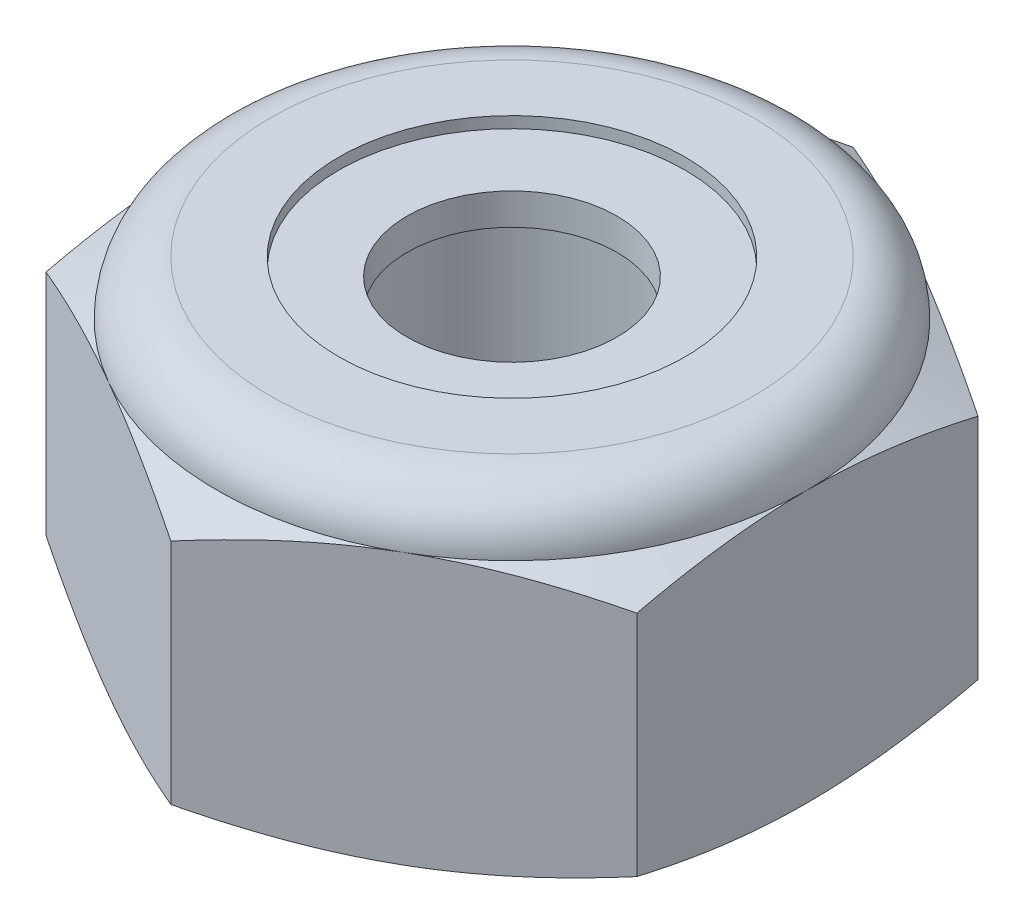
SolidWorks part; units mm, degrees
ref_plane "Front" through (0, 0, 0) normal (0, 0, 1) x (1, 0, 0)
ref_plane "Top" through (0, 0, 0) normal (0, 1, 0) x (1, 0, 0)
ref_plane "Right" through (0, 0, 0) normal (1, 0, 0) x (0, 0, -1)
sketch "Sketch1" plane through (0, 0, 0) normal (0, 1, 0) x (1, 0, 0)
  line L1 (0, 4.5827) -> (-3.9688, 2.2914)
  line L2 (-3.9688, 2.2914) -> (-3.9688, -2.2914)
  line L3 (-3.9688, -2.2914) -> (0, -4.5827)
  line L4 (0, -4.5827) -> (3.9688, -2.2914)
  line L5 (3.9688, -2.2914) -> (3.9687, 2.2914)
  line L6 (3.9687, 2.2914) -> (0, 4.5827)
  circle A0 centre (0, 0) radius 3.9688 construction
  dimension "Hex Flats" = 7.9375
extrude "Extrude1" add sketch "Sketch1" along normal blind 4.3656
sketch "Sketch2" plane through (0, 0, 0) normal (1, 0, 0) x (0, 0, -1)
  line L0 (-1.7526, 0) -> (-1.7526, 4.3656) construction
  line L1 (0, 0) -> (1.7526, 0)
  line L2 (0, 0) -> (0, 4.3656)
  line L3 (0, 4.3656) -> (1.7526, 4.3656)
  line L4 (1.7526, 0) -> (1.7526, 4.3656)
  line L5 (-2.2914, 4.3656) -> (2.2914, 4.3656) construction
  line L7 (0, -1.7526) -> (0, 0) construction
  dimension "Thread Dia" = 3.5052
revolve "Revolve1" add sketch "Sketch2" angle 360 about L7
sketch "Sketch3" plane through (0, 0, 0) normal (1, 0, 0) x (0, 0, -1)
  line L0 (1.7526, 4.3656) -> (-1.7526, 4.3656) construction
  line L1 (-1.7526, 4.3656) -> (-1.7526, 3.5719) construction
  line L2 (-1.7526, 3.5719) -> (1.7526, 4.3656) construction
  line L3 (1.7526, 4.3656) -> (1.7745, 4.2689) construction
  line L4 (1.7745, 4.2689) -> (1.9279, 3.5915)
  line L5 (1.9279, 3.5915) -> (1.4541, 3.7385)
  line L6 (1.4541, 3.7385) -> (1.4103, 3.932)
  line L7 (1.4103, 3.932) -> (1.7745, 4.2689)
  line L8 (1.4322, 3.8353) -> (1.8512, 3.9302) construction
  line L9 (1.7526, 4.3656) -> (1.7526, 3.9078) construction
  line L10 (1.7526, 3.9078) -> (-1.7526, 3.1141) construction
  line L11 (-1.7526, 3.1141) -> (-1.7526, 3.5719) construction
  line L12 (-0.1935, 4.3656) -> (0.1935, 2.6563) construction
  line L13 (-1.7526, 0) -> (-1.7526, 4.3656) construction
  line L14 (0, 4.3656) -> (1.7526, 4.3656) construction
  line L15 (1.7526, 0) -> (1.7526, 4.3656) construction
  point P13 (0, 3.511)
  dimension "D1" = 0.0992
  dimension "D2" = 0.1984
  dimension "Thread Pitch" = 0.7937
  dimension "D4" = 60
  dimension "D5" = 0.7937
revolve "Cut-Revolve1" [suppressed] cut sketch "Sketch3" angle 360 about L12
pattern_linear "LPattern1" [suppressed] count 6 spacing 0.7937 along (0, 1, 0) count 2 spacing 0.7937 along (0, 1, 0)
sketch "Sketch4" plane through (0, 0, 0) normal (1, 0, 0) x (0, 0, -1)
  line L0 (0, 4.3656) -> (1.7526, 4.3656)
  line L1 (1.7526, 4.3656) -> (1.4103, 4.206)
  line L2 (1.4103, 4.206) -> (1.4103, 0.1596)
  line L3 (1.4103, 0.1596) -> (1.7526, 0)
  line L4 (1.7526, 0) -> (0, 0)
  line L5 (0, 0) -> (0, 4.3656)
  line L6 (1.7526, 0) -> (1.7526, 4.3656) construction
  line L7 (0, 4.3656) -> (1.7526, 4.3656) construction
  line L8 (0, 0) -> (1.7526, 0) construction
  line L9 (0, 0) -> (0, 4.3656) construction
  line L10 (0, 4.3656) -> (0, 4.7433) construction
  dimension "D1" = 25
revolve "Cut-Revolve2" cut sketch "Sketch4" angle 360 about L10
combine bodies "Combine1" operation type subtract main body 112 bodies to subtract 109
sketch "Sketch5" plane through (0, 0, 0) normal (1, 0, 0) x (0, 0, -1)
  line L0 (0, 0) -> (3.9688, 0)
  line L1 (3.9688, 0) -> (4.5827, 0.2863)
  line L2 (4.5827, 0.2863) -> (4.5827, 3.3517)
  line L3 (4.5827, 3.3517) -> (3.9688, 3.638)
  line L4 (3.2411, 4.3656) -> (3.2411, 5.6356)
  line L5 (3.2411, 5.6356) -> (5.8527, 5.6356)
  line L6 (5.8527, 5.6356) -> (5.8527, -1.27)
  line L7 (5.8527, -1.27) -> (0, -1.27)
  line L8 (0, -1.27) -> (0, 0)
  line L9 (3.9688, 3.638) -> (3.9688, 0) construction
  line L10 (0, 0) -> (1.7526, 0) construction
  line L13 (4.5827, 1.819) -> (5.8527, 1.819) construction
  line L14 (4.5827, 4.3656) -> (4.5827, 0) construction
  line L15 (0, 0) -> (0, 5.6356) construction
  line L20 (0, 5.6356) -> (3.2411, 5.6356) construction
  line L22 (0, 4.3656) -> (1.7526, 4.3656) construction
  arc A0 (3.9688, 3.638) -> (3.2411, 4.3656) centre (3.2411, 3.638) ccw
  dimension "D1" = 25
  dimension "D2" = 1.27
  dimension "D3" = 4.3656
  dimension "D4" = 0.7276
revolve "Cut-Revolve3" cut sketch "Sketch5" angle 360 about L15
sketch "Sketch6" plane through (0, 0, 0) normal (1, 0, 0) x (0, 0, -1)
  line L0 (0, 3.638) -> (3.8164, 3.638)
  line L1 (3.2411, 4.2132) -> (2.3257, 4.2132)
  line L2 (0, 5.6356) -> (0, 3.638)
  line L3 (2.3257, 5.6356) -> (0, 5.6356)
  line L4 (0, 5.6356) -> (3.2411, 5.6356) construction
  line L5 (0, 0) -> (0, 5.6356) construction
  line L6 (0, 5.6356) -> (0, 44.323) construction
  line L7 (2.3257, 4.2132) -> (2.3257, 5.6356)
  line L8 (3.2411, 4.3656) -> (3.2411, 4.2132) construction
  line L9 (2.3257, 4.2132) -> (1.4103, 4.2132) construction
  line L10 (1.4103, 4.2132) -> (1.4103, 4.206) construction
  arc A0 (3.8164, 3.638) -> (3.2411, 4.2132) centre (3.2411, 3.638) ccw
  arc A1 (3.9688, 3.638) -> (3.2411, 4.3656) centre (3.2411, 3.638) ccw construction
  dimension "D1" = 0.1524
revolve "Cut-Revolve4" cut sketch "Sketch6" angle 360 about L6
sketch "Sketch7" plane through (0, 0, 0) normal (1, 0, 0) x (0, 0, -1)
  line L0 (1.4103, 3.7142) -> (3.7343, 3.7142)
  line L1 (3.2411, 4.137) -> (1.4103, 4.137)
  line L2 (1.4103, 4.137) -> (1.4103, 3.7142)
  line L3 (1.4103, 3.7142) -> (0, 3.7142) construction
  line L4 (0, 3.7142) -> (0, 4.137) construction
  line L5 (0, 4.137) -> (1.4103, 4.137) construction
  line L6 (1.4103, 3.7142) -> (1.4103, 3.638) construction
  line L7 (0, 3.638) -> (3.8164, 3.638) construction
  line L8 (3.2411, 4.137) -> (3.2411, 4.2132) construction
  arc A0 (3.7343, 3.7142) -> (3.2411, 4.137) centre (3.2411, 3.638) ccw
  arc A2 (3.8164, 3.638) -> (3.2411, 4.2132) centre (3.2411, 3.638) ccw construction
  dimension "D1" = 0.0762
revolve "Revolve2" add sketch "Sketch7" angle 360 about L4
equation "\"D1@Sketch3\"=\"Thread Pitch@Sketch3\"/8"
equation "\"D2@Sketch3\"=\"Thread Pitch@Sketch3\"/4"
equation "\"D5@Sketch3\"=\"Thread Pitch@Sketch3\""
equation "\"D4@LPattern1\"=\"Thread Pitch@Sketch3\""
equation "\"D3@LPattern1\"=\"Thread Pitch@Sketch3\""
equation "\"D1@LPattern1\"=\"Height@Extrude1\"/\"Thread Pitch@Sketch3\""
equation "\"D4@Sketch5\"=\"Height@Extrude1\"/6"
